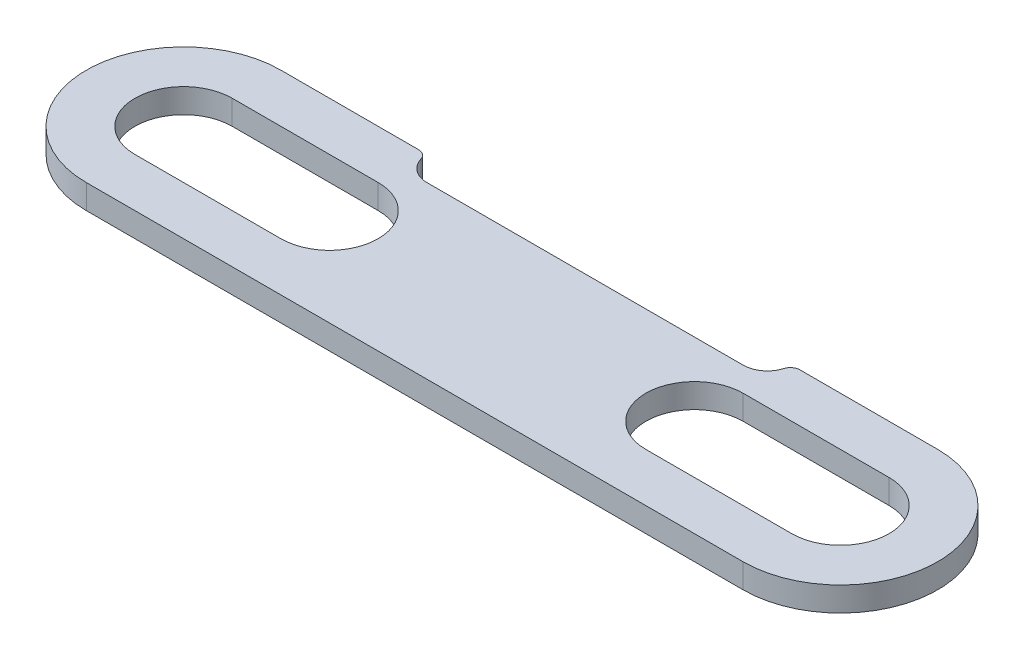
SolidWorks part; units mm, degrees
ref_plane "Front Plane" through (0, 0, 0) normal (0, 0, 1) x (1, 0, 0)
ref_plane "Top Plane" through (0, 0, 0) normal (0, 1, 0) x (1, 0, 0)
ref_plane "Right Plane" through (0, 0, 0) normal (1, 0, 0) x (0, 0, -1)
sketch "Sketch1" plane through (0, 0, 0) normal (0, 1, 0) x (1, 0, 0)
  line L0 (-111.125, 0) -> (111.125, 0) construction
  line L1 (0, 25.4) -> (0, -25.4) construction
  line L2 (-85.725, 0) -> (85.725, 0) construction
  line L3 (-85.725, 25.4) -> (85.725, 25.4)
  line L4 (-85.725, -25.4) -> (85.725, -25.4)
  line L5 (-47.625, 0) -> (47.625, 0) construction
  line L6 (-85.725, 0) -> (85.725, 0) construction
  line L7 (-85.725, 0) -> (-47.625, 0) construction
  line L8 (-85.725, 12.7) -> (-47.625, 12.7)
  line L9 (-85.725, -12.7) -> (-47.625, -12.7)
  line L10 (85.725, 0) -> (47.625, 0) construction
  line L11 (85.725, 12.7) -> (47.625, 12.7)
  line L12 (85.725, -12.7) -> (47.625, -12.7)
  line L13 (-47.625, 12.7) -> (-47.625, 25.4) construction
  line L14 (47.625, 12.7) -> (47.625, 25.4) construction
  arc A0 (-85.725, 25.4) -> (-85.725, -25.4) centre (-85.725, 0) ccw
  arc A1 (85.725, -25.4) -> (85.725, 25.4) centre (85.725, 0) ccw
  arc A2 (-85.725, 12.7) -> (-85.725, -12.7) centre (-85.725, 0) ccw
  arc A3 (-47.625, -12.7) -> (-47.625, 12.7) centre (-47.625, 0) ccw
  arc A4 (85.725, 12.7) -> (85.725, -12.7) centre (85.725, 0) cw
  arc A5 (47.625, -12.7) -> (47.625, 12.7) centre (47.625, 0) cw
  point P3 (0, 0)
  point P4 (0, 0)
  point P8 (0, 0)
  point P10 (0, 0)
  point P20 (0, 0)
  point P21 (0, 0)
  point P23 (-66.675, 0)
  point P30 (66.675, 0)
  dimension "D1" = 222.25
  dimension "D2" = 50.8
  dimension "D3" = 95.25
  dimension "D4" = 171.45
  dimension "D5" = 25.4
extrude "Boss-Extrude1" add sketch "Sketch1" along normal mid plane 6.35
sketch "Sketch2" plane through (0, 3.175, 0) normal (0, 1, 0) x (1, 0, 0)
  line L0 (-41.275, 25.4) -> (41.275, 25.4) construction
  line L1 (-85.725, 25.4) -> (85.725, 25.4) construction
  line L3 (-41.275, 19.05) -> (41.275, 19.05)
  line L4 (-47.625, 25.4) -> (47.625, 25.4)
  arc A0 (-47.625, 25.4) -> (-41.275, 19.05) centre (-41.275, 25.4) ccw
  arc A1 (41.275, 19.05) -> (47.625, 25.4) centre (41.275, 25.4) ccw
  point P5 (0, 25.4)
  dimension "D2" = 95.25
extrude "Cut-Extrude1" cut sketch "Sketch2" against normal through all
fillet "Fillet1" radius 2.54 2 edges at (47.625, 0, -25.4) (-47.625, 0, -25.4)
